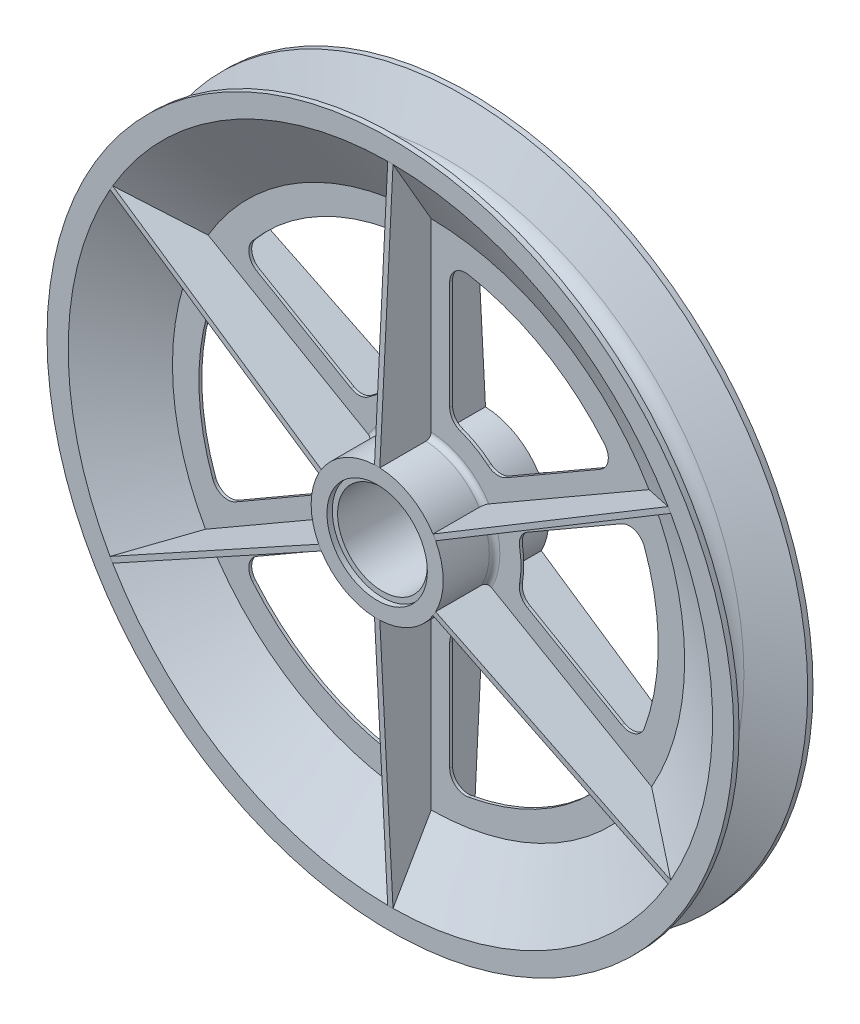
SolidWorks part; units mm, degrees
material "ABS"
ref_plane "Front Plane" through (0, 0, 0) normal (0, 0, 1) x (1, 0, 0)
ref_plane "Top Plane" through (0, 0, 0) normal (0, 1, 0) x (1, 0, 0)
ref_plane "Right Plane" through (0, 0, 0) normal (1, 0, 0) x (0, 0, -1)
sketch "Sketch1" plane through (0, 0, 0) normal (0, 0, 1) x (1, 0, 0)
  circle A0 centre (0, 0) radius 650
  dimension "D1" = 1300
extrude "Boss-Extrude1" add sketch "Sketch1" against normal mid plane 150
sketch "Sketch2" plane through (0, 0, 0) normal (0, 0, 1) x (1, 0, 0)
  circle A0 centre (0, 0) radius 480
  point P5 (10, 125)
  point P6 (10, 620)
  point P7 (-10, 125)
  point P8 (-10, 620)
extrude "Cut-Extrude1" cut sketch "Sketch2" against normal through all draft 60 draft outward yes
mirror "Mirror1" about plane through (0, 0, 0) normal (0, 0, 1) of "Cut-Extrude1"
sketch "Sketch3" plane through (0, 0, 0) normal (0, 0, 1) x (1, 0, 0)
  circle A0 centre (0, 0) radius 125
  dimension "D1" = 250
extrude "Boss-Extrude2" add sketch "Sketch3" along normal mid plane 200 separate body
ref_plane "Plane1" through (0, 0, 100) normal (0, 0, 1) x (1, 0, 0)
sketch "Sketch4" plane through (0, 0, 100) normal (0, 0, 1) x (1, 0, 0)
  circle A0 centre (0, 0) radius 95
  dimension "D1" = 190
extrude "Cut-Extrude2" cut sketch "Sketch4" against normal blind 10
mirror "Mirror2" about plane through (0, 0, 0) normal (0, 0, 1) of "Cut-Extrude2"
sketch "Sketch5" plane through (0, 0, 100) normal (0, 0, 1) x (1, 0, 0)
  circle A0 centre (0, 0) radius 85
  dimension "D1" = 170
extrude "Cut-Extrude3" cut sketch "Sketch5" against normal through all
sketch "Sketch6" plane through (0, 0, 0) normal (0, 0, 1) x (1, 0, 0)
  circle A0 centre (0, 0) radius 85 construction
  circle A1 centre (0, 0) radius 85
  circle A4 centre (0, 0) radius 485
extrude "Boss-Extrude3" add sketch "Sketch6" along normal mid plane 5.5
fillet "Fillet1" radius 10 2 edges at (125, 0, -2.75) (125, 0, 2.75)
sketch "Sketch7" plane through (0, 0, 0) normal (0, 0, 1) x (1, 0, 0)
  line L13 (40, 398.6643) -> (40, 192.6785)
  line L14 (325.2534, 233.9732) -> (146.8645, 130.9803)
  arc A0 (40, 192.6785) -> (59.7561, 164.4816) centre (70, 192.6785) ccw
  arc A1 (112.5672, 133.9911) -> (146.8645, 130.9803) centre (131.8645, 156.961) ccw
  arc A3 (325.2534, 233.9732) -> (333.2486, 279.221) centre (310.2534, 259.9539) ccw
  arc A4 (112.5672, 133.9911) -> (59.7561, 164.4816) centre (0, 0) ccw
  arc A5 (333.2486, 279.221) -> (75.1882, 428.2122) centre (0, 0) ccw
  arc A6 (75.1882, 428.2122) -> (40, 398.6643) centre (70, 398.6643) ccw
  point P34 (0, 0)
  dimension "D1" = 30
extrude "Cut-Extrude4" cut sketch "Sketch7" along normal through all both and the other way through all
pattern_circular "CirPattern1" count 6 over 360 about axis through (0, 0, 0) along (0, 0, 1) of "Cut-Extrude4"
sketch "Sketch8" plane through (0, 0, 0) normal (1, 0, 0) x (0, 0, -1)
  line L0 (-75, 609.9038) -> (-100, 125)
  line L1 (-2.75, 484.7631) -> (-75, 609.9038) construction
  line L2 (-2.75, 484.7631) -> (-2.75, -484.7631) construction
  line L4 (-2.75, 484.7631) -> (-75, 609.9038)
  line L5 (-2.75, 484.7631) -> (-2.75, 115)
  line L6 (-100, 125) -> (-100, 115)
  line L7 (-2.75, 115) -> (-100, 115)
extrude "Boss-Extrude4" add sketch "Sketch8" along normal mid plane 10
pattern_circular "CirPattern2" count 6 over 360 about axis through (0, 0, 0) along (0, 0, 1) of "Boss-Extrude4"
mirror "Mirror3" about plane through (0, 0, 0) normal (0, 0, 1) of "CirPattern2", "Boss-Extrude4"
sketch "Sketch9" plane through (0, 0, 0) normal (1, 0, 0) x (0, 0, -1)
  line L2 (75, 650) -> (-75, 650) construction
  line L3 (-65, 650) -> (-28.7256, 563.8392)
  line L4 (65, 650) -> (30.0321, 564.1791)
  line L5 (0, 0) -> (1.5014, 696.059) construction
  line L6 (-65, 650) -> (65, 650)
  arc A0 (30.0321, 564.1791) -> (-28.7256, 563.8392) centre (0.5828, 576.1783) cw
  point P14 (1.0636, 493.0823)
  dimension "D4" = 31.8
  dimension "D3" = 45
revolve "Cut-Revolve1" cut sketch "Sketch9" angle 360 about axis through (0, 0, 0) along (0, 0, 1)
scale "Scale2" scale about centroid uniform scaling yes scale factor 0.035294
